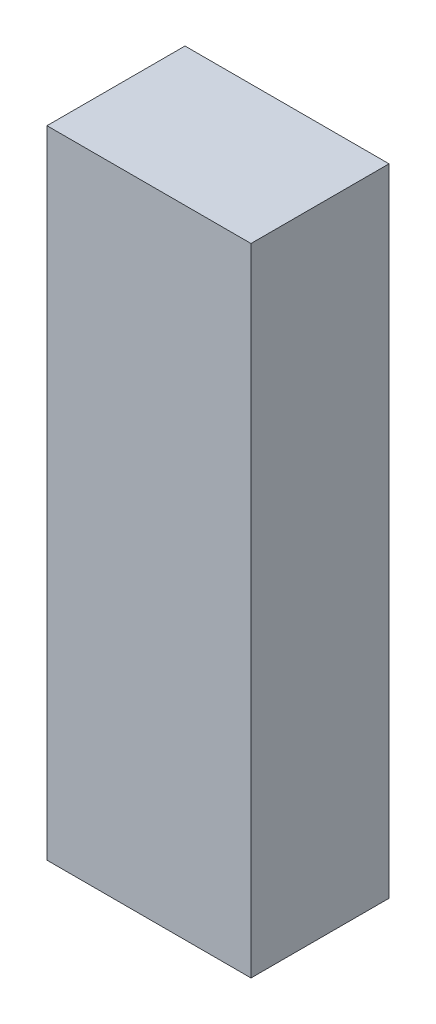
SolidWorks part; units mm, degrees
ref_plane "Front" through (0, 0, 0) normal (0, 0, 1) x (1, 0, 0)
ref_plane "Top" through (0, 0, 0) normal (0, 1, 0) x (1, 0, 0)
ref_plane "Right" through (0, 0, 0) normal (1, 0, 0) x (0, 0, -1)
sketch "Sketch1" plane through (0, 0, 0) normal (0, 0, 1) x (1, 0, 0)
  line L0 (0, 0) -> (0, 106)
  line L1 (0, 106) -> (34, 106)
  line L2 (34, 106) -> (34, 0)
  line L3 (34, 0) -> (0, 0)
extrude "Boss-Extrude1" add sketch "Sketch1" along normal blind 23
